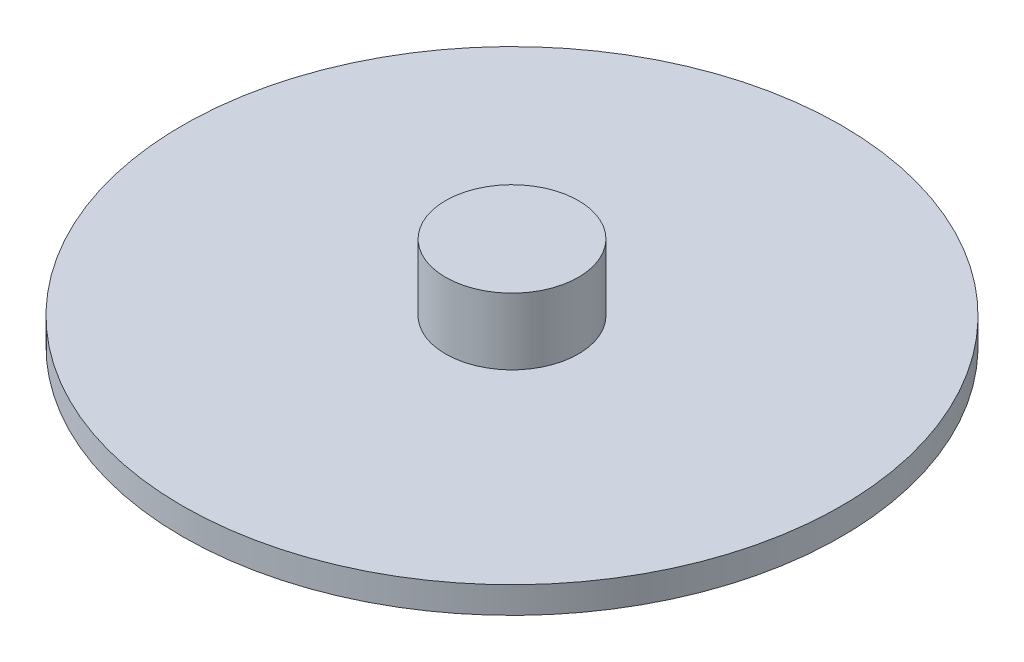
SolidWorks part; units mm, degrees
ref_plane "Front Plane" through (0, 0, 0) normal (0, 0, 1) x (1, 0, 0)
ref_plane "Top Plane" through (0, 0, 0) normal (0, 1, 0) x (1, 0, 0)
ref_plane "Right Plane" through (0, 0, 0) normal (1, 0, 0) x (0, 0, -1)
sketch "Sketch1" plane through (0, 0, 0) normal (0, 1, 0) x (1, 0, 0)
  circle A0 centre (0, 0) radius 31.496
  dimension "D1" = 62.992
extrude "Boss-Extrude1" add sketch "Sketch1" along normal blind 2.54
sketch "Sketch2" plane through (0, 2.54, 0) normal (0, 1, 0) x (1, 0, 0)
  circle A0 centre (0, 0) radius 6.35
  dimension "D1" = 12.7
extrude "Boss-Extrude2" add sketch "Sketch2" along normal blind 6.35
